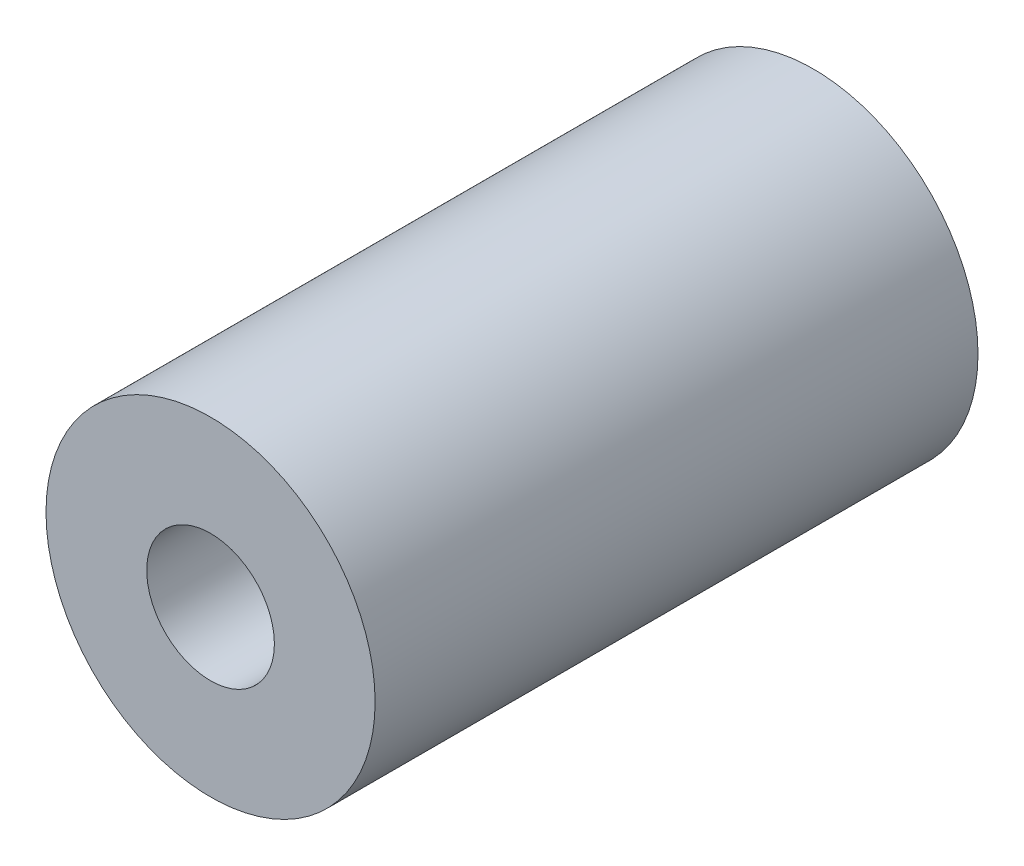
SolidWorks part; units mm, degrees
material "KNSU"
ref_plane "Alzado" through (0, 0, 0) normal (0, 0, 1) x (1, 0, 0)
ref_plane "Planta" through (0, 0, 0) normal (0, 1, 0) x (1, 0, 0)
ref_plane "Vista lateral" through (0, 0, 0) normal (1, 0, 0) x (0, 0, -1)
sketch "Croquis1" plane through (0, 0, 0) normal (0, 0, 1) x (1, 0, 0)
  circle A0 centre (0, 0) radius 23.2
  circle A1 centre (0, 0) radius 9
  dimension "D1" = 46.4
  dimension "D2" = 18
extrude "Saliente-Extruir1" add sketch "Croquis1" along normal blind 85
equation "\"ODGrain\" = 46.4"
equation "\"D1@Croquis1\"= \"ODGrain\""
equation "\"IDGrain\" = 18"
equation "\"D2@Croquis1\"=\"IDGrain\""
equation "\"LengthGrain\" = 85"
equation "\"D1@Saliente-Extruir1\"=\"LengthGrain\""
